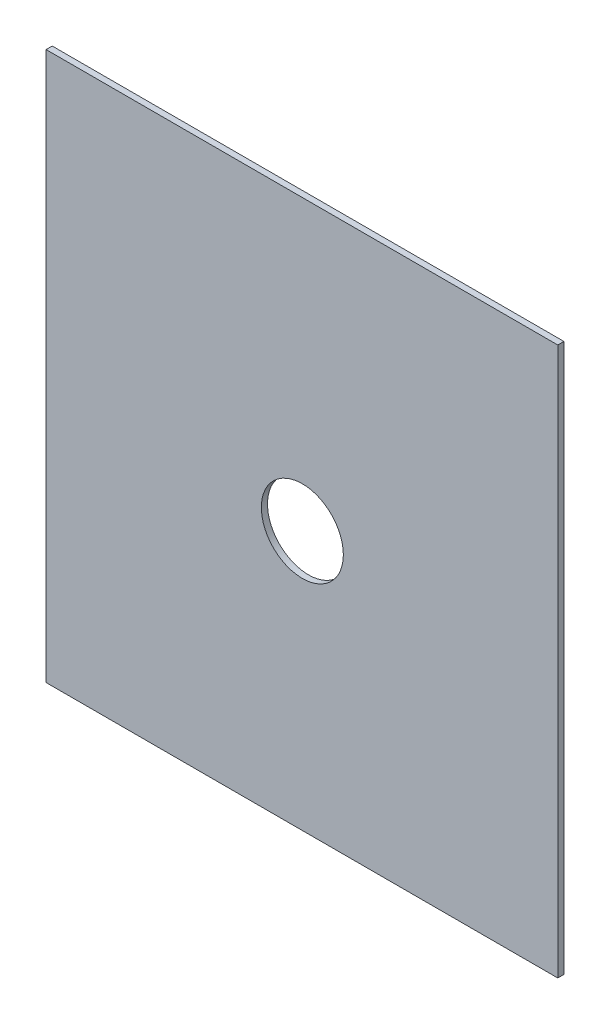
SolidWorks part; units mm, degrees
ref_plane "Front Plane" through (0, 0, 0) normal (0, 0, 1) x (1, 0, 0)
ref_plane "Top Plane" through (0, 0, 0) normal (0, 1, 0) x (1, 0, 0)
ref_plane "Right Plane" through (0, 0, 0) normal (1, 0, 0) x (0, 0, -1)
sketch "Sketch1" plane through (0, 0, 0) normal (0, 0, 1) x (1, 0, 0)
  line L0 (62.5, -267.4) -> (0, -267.4) construction
  line L1 (0, 0) -> (249.6, 0)
  line L2 (0, 0) -> (0, -267.4)
  line L3 (0, -267.4) -> (249.6, -267.4)
  line L4 (249.6, 0) -> (249.6, -267.4)
  dimension "D2" = 249.6
extrude "Boss-Extrude1" add sketch "Sketch1" along normal blind 3
sketch "Sketch2" plane through (0, 0, 3) normal (0, 0, 1) x (1, 0, 0)
  line L0 (125, 0) -> (125, -350.4) construction
  circle A0 centre (125, -140.911) radius 20
  dimension "D1" = 40
extrude "Cut-Extrude1" cut sketch "Sketch2" against normal through all
